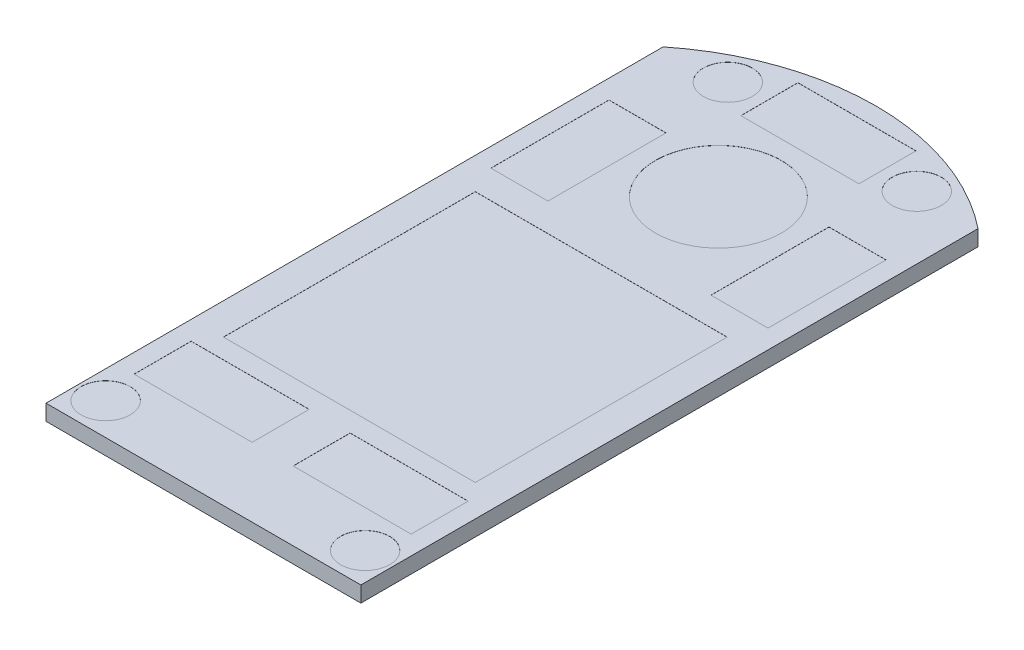
SolidWorks part; units mm, degrees
material "Silicon Rubber"
ref_plane "Front Plane" through (0, 0, 0) normal (0, 0, 1) x (1, 0, 0)
ref_plane "Top Plane" through (0, 0, 0) normal (0, 1, 0) x (1, 0, 0)
ref_plane "Right Plane" through (0, 0, 0) normal (1, 0, 0) x (0, 0, -1)
sketch "Sketch1" plane through (0, 0, 0) normal (0, 1, 0) x (1, 0, 0)
  line L1 (-31.75, 0) -> (31.75, 0)
  line L2 (-31.75, 0) -> (-31.75, 111.76)
  line L4 (31.75, 0) -> (31.75, 111.76)
  arc A0 (-31.75, 111.76) -> (31.75, 111.76) centre (0, 72.1043) cw
  point P4 (0, 0)
  dimension "D2" = 50.8
  dimension "D1" = 111.76
  dimension "D3" = 63.5
extrude "Boss-Extrude1" add sketch "Sketch1" along normal blind 12.7 contours L2 A0 L4 L1
sketch "Sketch2" plane through (-31.75, 0, 0) normal (-1, 0, 0) x (0, 0, 1)
  line L7 (0, 0) -> (-111.76, 0) construction
  line L8 (0, 12.7) -> (0, 0) construction
  line L9 (0, 0) -> (12.7, 0)
  line L10 (0, 0) -> (0, 12.7)
  arc A2 (12.7, 0) -> (0, 12.7) centre (12.7, 12.7) ccw
  point P2 (12.7, 0)
  point P3 (0, 12.7)
  dimension "D2" = 0
  dimension "D1" = 25.4
  dimension "D3" = 0
  dimension "D4" = 12.7
  dimension "D5" = 12.7
extrude "Boss-Extrude2" add sketch "Sketch2" against normal blind 11.43
mirror "Mirror1" about plane through (0, 0, 0) normal (1, 0, 0) of "Boss-Extrude2"
sketch "Sketch24" plane through (0, 0, 0) normal (0, -1, 0) x (1, 0, 0)
  line L7 (20.32, 0) -> (-20.32, 0)
  line L8 (-20.32, 0) -> (-20.32, 12.7)
  line L9 (-20.32, 12.7) -> (-31.75, 12.7)
  line L10 (-31.75, 12.7) -> (-31.75, -111.76)
  line L11 (31.75, -111.76) -> (31.75, 12.7)
  line L12 (31.75, 12.7) -> (20.32, 12.7)
  line L13 (20.32, 12.7) -> (20.32, 0)
  line L14 (20.32, 0) -> (-20.32, 0)
  line L15 (-20.32, 0) -> (-20.32, 12.7)
  line L16 (-20.32, 12.7) -> (-31.75, 12.7)
  line L17 (-31.75, 12.7) -> (-31.75, -111.76)
  line L18 (31.75, -111.76) -> (31.75, 12.7)
  line L19 (31.75, 12.7) -> (20.32, 12.7)
  line L20 (20.32, 12.7) -> (20.32, 0)
  arc A1 (-31.75, -111.76) -> (31.75, -111.76) centre (0, -72.1043) ccw
  arc A2 (-31.75, -111.76) -> (31.75, -111.76) centre (0, -72.1043) ccw
  dimension "D1" = 0
extrude "Boss-Extrude3" add sketch "Sketch24" along normal blind 3.175
ref_plane "Plane2" through (0, 0, 0) normal (0, -1, 0) x (-1, 0, 0)
sketch "Sketch25" plane through (0, 0, 0) normal (0, -1, 0) x (-1, 0, 0)
  line L1 (-38.7918, -31.2805) -> (62.8082, -31.2805)
  line L2 (-38.7918, -31.2805) -> (-38.7918, 171.9195)
  line L3 (-38.7918, 171.9195) -> (62.8082, 171.9195)
  line L4 (62.8082, -31.2805) -> (62.8082, 171.9195)
  dimension "D1" = 203.2
  dimension "D2" = 101.6
extrude "Cut-Extrude16" cut sketch "Sketch25" against normal through all
sketch "Sketch31" plane through (0, 0, 0) normal (0, 1, 0) x (1, 0, 0)
  line L1 (-20.32, 0) -> (20.32, 0)
  line L2 (-20.32, 0) -> (-20.32, -12.7)
  line L3 (-20.32, -12.7) -> (20.32, -12.7)
  line L4 (20.32, 0) -> (20.32, -12.7)
extrude "Boss-Extrude5" add sketch "Sketch31" against normal up to surface (3.175 mm away) up to face at (0, -3.175, -22.983)
sketch "Sketch27" plane through (0, 0, 0) normal (0, 1, 0) x (1, 0, 0)
  line L0 (0, 0) -> (0, 122.9043) construction
  line L2 (31.75, 0) -> (31.75, 111.76) construction
  line L3 (31.75, -12.7) -> (31.75, 111.76) construction
  line L4 (31.75, 55.88) -> (-31.75, 55.88) construction
  line L5 (-31.75, -12.7) -> (-31.75, 111.76) construction
  line L6 (31.75, -12.7) -> (-31.75, -12.7) construction
  line L7 (-25.4, 67.5323) -> (25.4, 67.5323)
  line L8 (-25.4, 67.5323) -> (-25.4, 16.7323)
  line L9 (-25.4, 16.7323) -> (25.4, 16.7323)
  line L10 (25.4, 67.5323) -> (25.4, 16.7323)
  arc A0 (31.75, 111.76) -> (-31.75, 111.76) centre (0, 72.1043) ccw construction
  circle A1 centre (19.05, 112.1093) radius 4.953
  circle A2 centre (-19.05, 112.1093) radius 4.953
  circle A3 centre (26.162, -6.2547) radius 4.953
  circle A5 centre (-26.162, -6.2547) radius 4.953
  circle A6 centre (0, 91.1543) radius 12.7
  point P30 (0, 67.5323)
  dimension "D1" = 9.906
  dimension "D4" = 9.906
  dimension "D7" = 5.588
  dimension "D8" = 25.4
  dimension "D5" = 118.364
  dimension "D2" = 10.795
  dimension "D3" = 12.7
  dimension "D6" = 12.7
  dimension "D9" = 31.75
  dimension "D10" = 50.8
  dimension "D11" = 55.372
extrude "Cut-Extrude17" cut sketch "Sketch27" against normal blind 0.0254
sketch "Sketch28" plane through (0, 0, 0) normal (0, 1, 0) x (1, 0, 0)
  line L0 (-31.75, -12.7) -> (-31.75, 111.76) construction
  line L1 (-27.94, 1.2541) -> (-4.1275, 1.2541)
  line L2 (-27.94, 1.2541) -> (-27.94, 12.7635)
  line L3 (-27.94, 12.7635) -> (-4.1275, 12.7635)
  line L4 (-4.1275, 1.2541) -> (-4.1275, 12.7635)
  line L5 (0, 122.9043) -> (0, 54.1496) construction
  line L8 (27.94, 97.028) -> (27.94, 73.2155)
  line L14 (0, 0) -> (0, 54.1496) construction
  line L15 (27.94, 1.2541) -> (27.94, 12.7635)
  line L16 (27.94, 1.2541) -> (4.1275, 1.2541)
  line L17 (4.1275, 1.2541) -> (4.1275, 12.7635)
  line L18 (27.94, 12.7635) -> (4.1275, 12.7635)
  line L23 (-11.9062, 107.5849) -> (11.9063, 107.5849)
  line L24 (-11.9062, 107.5849) -> (-11.9062, 119.0943)
  line L25 (-11.9062, 119.0943) -> (11.9063, 119.0943)
  line L26 (11.9063, 107.5849) -> (11.9063, 119.0943)
  line L27 (-11.9062, 107.5849) -> (11.9063, 119.0943) construction
  line L28 (-11.9062, 119.0943) -> (11.9063, 107.5849) construction
  line L29 (-27.94, 97.028) -> (-16.4306, 97.028)
  line L30 (-27.94, 97.028) -> (-27.94, 73.2155)
  line L31 (-27.94, 73.2155) -> (-16.4306, 73.2155)
  line L32 (-16.4306, 97.028) -> (-16.4306, 73.2155)
  line L33 (27.94, 73.2155) -> (16.4306, 73.2155)
  line L34 (16.4306, 97.028) -> (16.4306, 73.2155)
  line L35 (27.94, 97.028) -> (16.4306, 97.028)
  arc A0 (31.75, 111.76) -> (-31.75, 111.76) centre (0, 72.1043) ccw construction
  point P32 (0, 113.3396)
  point P41 (0, 0)
  point P42 (0, 0)
  dimension "D1" = 23.8125
  dimension "D2" = 11.5094
  dimension "D3" = 3.81
  dimension "D4" = 60.452
  dimension "D5" = 3.81
  dimension "D6" = 14.732
  dimension "D7" = 23.8125
  dimension "D8" = 11.5094
  dimension "D9" = 23.8125
  dimension "D10" = 11.5094
extrude "Cut-Extrude18" cut sketch "Sketch28" against normal blind 0.0254
